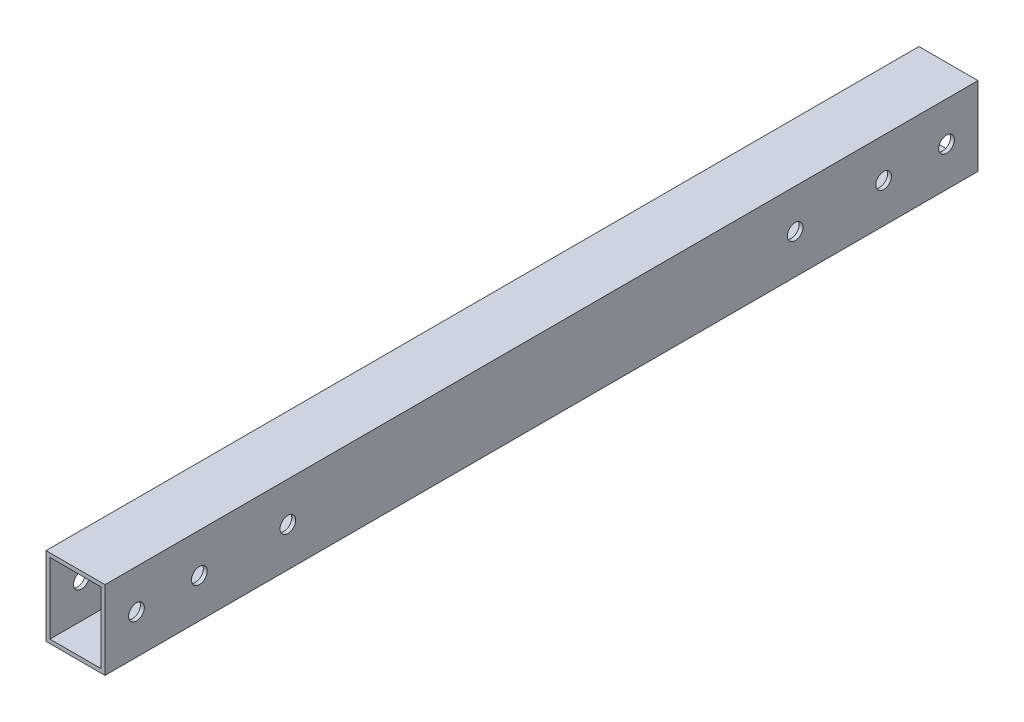
SolidWorks part; units mm, degrees
ref_plane "前视基准面" through (0, 0, 0) normal (0, 0, 1) x (1, 0, 0)
ref_plane "上视基准面" through (0, 0, 0) normal (0, 1, 0) x (1, 0, 0)
ref_plane "右视基准面" through (0, 0, 0) normal (1, 0, 0) x (0, 0, -1)
sketch "草图1" plane through (0, 0, 0) normal (0, 0, 1) x (1, 0, 0)
  line L0 (-18.0632, 19.3089) -> (11.9368, 19.3089)
  line L1 (11.9368, 19.3089) -> (11.9368, -20.6911)
  line L2 (11.9368, -20.6911) -> (-18.0632, -20.6911)
  line L3 (-18.0632, -20.6911) -> (-18.0632, 19.3089)
  line L4 (-18.0632, 19.3089) -> (-16.0632, 19.3089) construction
  line L5 (-16.0632, 19.3089) -> (-16.0632, 17.3089) construction
  line L6 (-16.0632, 17.3089) -> (9.9368, 17.3089)
  line L7 (9.9368, 17.3089) -> (9.9368, -18.6911)
  line L8 (9.9368, -18.6911) -> (-16.0632, -18.6911)
  line L9 (-16.0632, -18.6911) -> (-16.0632, 17.3089)
  dimension "D1" = 30
  dimension "D2" = 40
  dimension "D3" = 2
  dimension "D4" = 2
  dimension "D5" = 26
  dimension "D6" = 36
extrude "凸台-拉伸1" add sketch "草图1" along normal blind 444
sketch "草图2" plane through (-18.0632, 0, 0) normal (-1, 0, 0) x (0, 0, 1)
  line L0 (444, -0.6911) -> (428, -0.6911) construction
  line L1 (444, 19.3089) -> (444, -20.6911) construction
  line L2 (428, -0.6911) -> (396, -0.6911) construction
  line L3 (222, 19.3089) -> (222, -20.6911) construction
  line L4 (444, 19.3089) -> (0, 19.3089) construction
  line L5 (444, -20.6911) -> (0, -20.6911) construction
  line L6 (16, -0.6911) -> (48, -0.6911) construction
  line L7 (0, -0.6911) -> (16, -0.6911) construction
  line L8 (48, -0.6911) -> (63, -0.6911) construction
  line L9 (63, -50.1911) -> (63, 6.8089) construction
  line L10 (63, -0.6911) -> (93, -0.6911) construction
  circle A0 centre (396, -0.6911) radius 4
  circle A1 centre (428, -0.6911) radius 4
  circle A2 centre (16, -0.6911) radius 4
  circle A3 centre (48, -0.6911) radius 4
  circle A4 centre (93, -0.6911) radius 4
  circle A5 centre (351, -0.6911) radius 4
  dimension "D3" = 8
  dimension "D4" = 8
  dimension "D6" = 8
  dimension "D1" = 16
  dimension "D2" = 32
  dimension "D5" = 30
extrude "切除-拉伸1" cut sketch "草图2" against normal blind 96
ref_plane "基准面1" through (0, 0, 222) normal (0, 0, 1) x (1, 0, 0)
